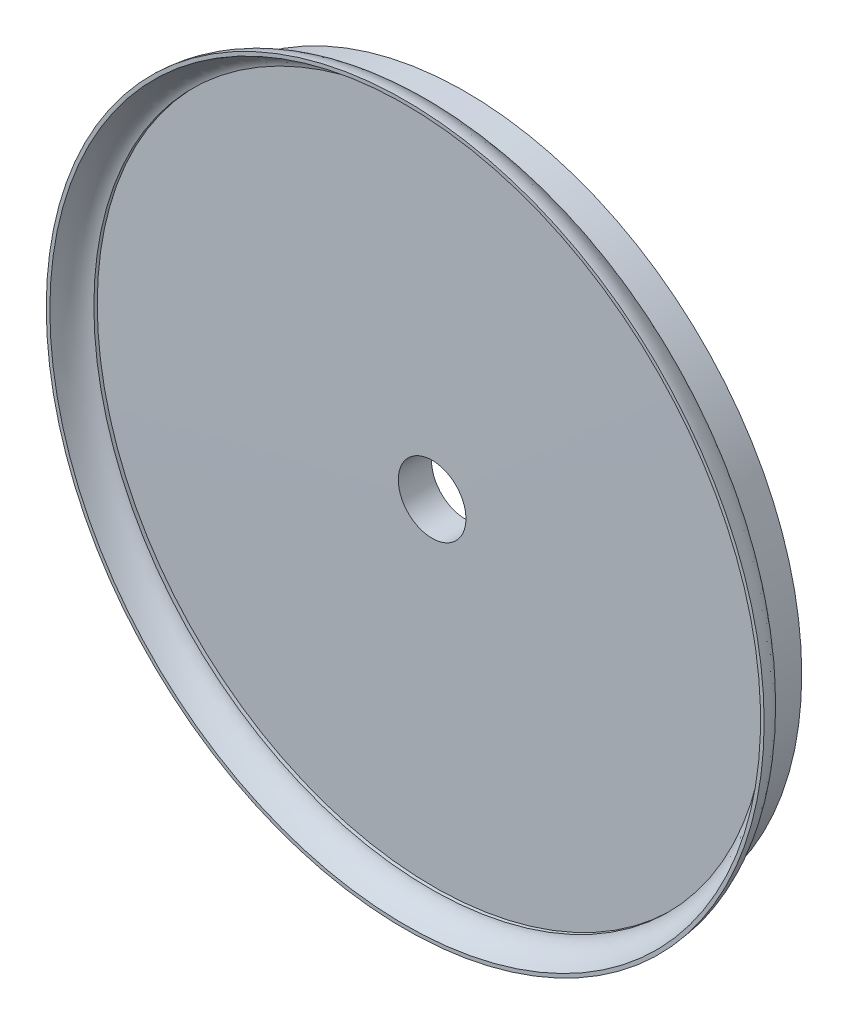
SolidWorks part; units mm, degrees
ref_plane "Front Plane" through (0, 0, 0) normal (0, 0, 1) x (1, 0, 0)
ref_plane "Top Plane" through (0, 0, 0) normal (0, 1, 0) x (1, 0, 0)
ref_plane "Right Plane" through (0, 0, 0) normal (1, 0, 0) x (0, 0, -1)
sketch "Sketch1" plane through (0, 0, 0) normal (0, 0, 1) x (1, 0, 0)
  circle A0 centre (0, 0) radius 44.75
  dimension "D1" = 89.5
extrude "Boss-Extrude1" add sketch "Sketch1" along normal blind 4
sketch "Sketch2" plane through (0, 0, 4) normal (0, 0, 1) x (1, 0, 0)
  circle A0 centre (0, 0) radius 47.75
  circle A1 centre (0, 0) radius 44.75 construction
  dimension "D1" = 3
extrude "Boss-Extrude2" add sketch "Sketch2" along normal blind 4
sketch "Sketch3" plane through (0, 0, 0) normal (1, 0, 0) x (0, 0, -1)
  line L0 (-4, -47.75) -> (-4, 47.75) construction
  line L1 (-4, -44.75) -> (-4, 44.75) construction
  line L2 (-4, 47.75) -> (-4, 44.75)
  line L3 (-4, 47.75) -> (-8, 47.75)
  line L4 (-14.6181, 0) -> (8.5023, 0) construction
  spline S0 degree 2 poles (-4, 44.75) (-5.5166, 47.7003) (-8, 47.75) knots 0 0 0 0.966898 0.966898 0.966898
revolve "Cut-Revolve1" cut sketch "Sketch3" angle 360 about L4
sketch "Sketch4" plane through (0, 0, 0) normal (1, 0, 0) x (0, 0, -1)
  line L1 (-8, 47.75) -> (-8, -47.75) construction
  line L2 (-4.6679, 44.75) -> (-4.2176, 44.75)
  line L3 (-4.2176, 44.75) -> (-4.4427, 0)
  line L4 (-4.4427, 0) -> (-8, 0)
  line L5 (-8, 0) -> (-8, 47.2729)
  spline S0 degree 2 poles (-8, 47.2729) (-5.0207, 46.3587) (-4.6679, 44.75) knots 0 0 0 0.527215 0.527215 0.527215
revolve "Cut-Revolve3" cut sketch "Sketch4" angle 360 about L4
sketch "Sketch5" plane through (0, 0, 0) normal (0, 0, -1) x (-1, 0, 0)
  circle A0 centre (0, 0) radius 4.5
  dimension "D1" = 9
extrude "Cut-Extrude1" cut sketch "Sketch5" against normal blind 10
